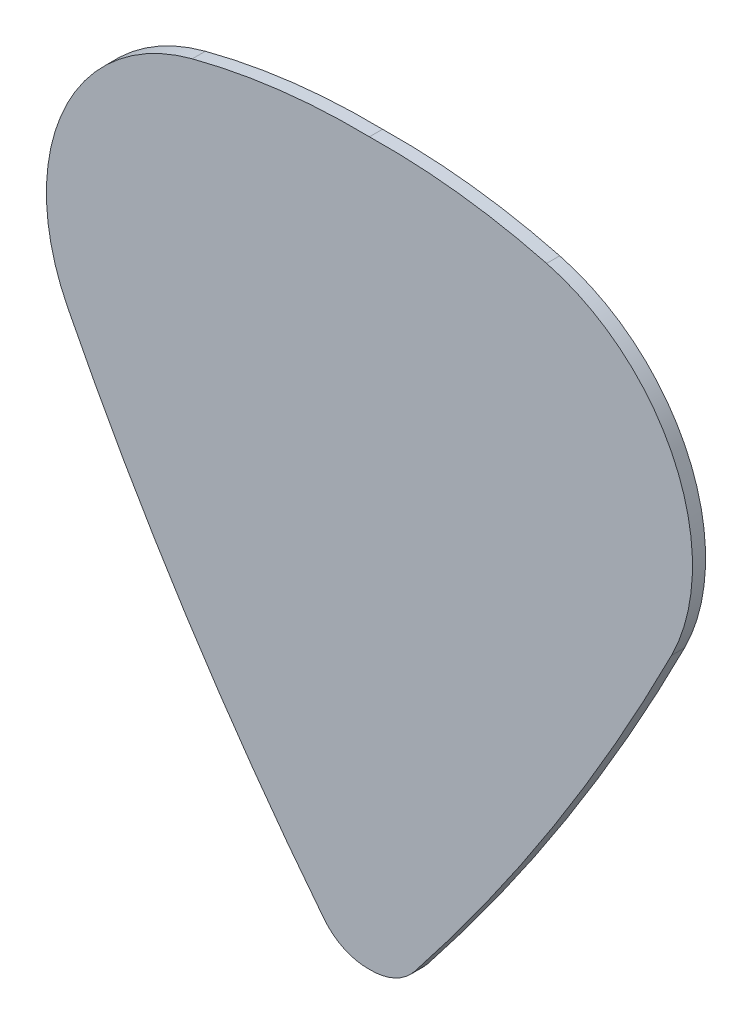
SolidWorks part; units mm, degrees
ref_plane "Front Plane" through (0, 0, 0) normal (0, 0, 1) x (1, 0, 0)
ref_plane "Top Plane" through (0, 0, 0) normal (0, 1, 0) x (1, 0, 0)
ref_plane "Right Plane" through (0, 0, 0) normal (1, 0, 0) x (0, 0, -1)
sketch "Sketch2" plane through (0, 0, 0) normal (0, 0, 1) x (1, 0, 0)
  line L0 (0, 16.1573) -> (0, -16.8349) construction
  line L1 (-13.8207, 2.5183) -> (0, 2.5183) construction
  arc A0 (2.0742, -15.8715) -> (0, -16.8349) centre (0.0817, -14.2963) cw
  arc A1 (-13.8207, 2.5183) -> (-8.1064, 15.1951) centre (-5.844, 6.549) cw
  arc A2 (-8.1064, 15.1951) -> (0, 16.1573) centre (-0.5834, -13.555) cw
  arc A3 (13.8207, 2.5183) -> (2.0742, -15.8715) centre (-83.1996, 51.5435) cw
  arc A4 (13.8207, 2.5183) -> (8.1064, 15.1951) centre (5.844, 6.549) ccw
  arc A5 (-13.8207, 2.5183) -> (-2.0742, -15.8715) centre (83.1996, 51.5435) ccw
  arc A6 (8.1064, 15.1951) -> (0, 16.1573) centre (0.5834, -13.555) ccw
  arc A7 (-2.0742, -15.8715) -> (0, -16.8349) centre (-0.0817, -14.2963) ccw
  dimension "D2" = 2.54
extrude "Boss-Extrude2" add sketch "Sketch2" along normal blind 0.6
